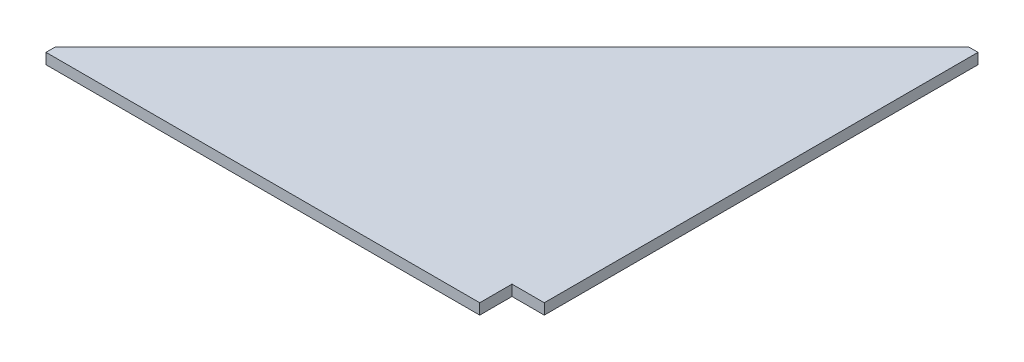
SolidWorks part; units mm, degrees
material "Pine"
ref_plane "Front Plane" through (0, 0, 0) normal (0, 0, 1) x (1, 0, 0)
ref_plane "Top Plane" through (0, 0, 0) normal (0, 1, 0) x (1, 0, 0)
ref_plane "Right Plane" through (0, 0, 0) normal (1, 0, 0) x (0, 0, -1)
sketch "Sketch1" plane through (0, 0, 0) normal (0, 1, 0) x (1, 0, 0)
  line L11 (-11.2, 550.1) -> (-550.1, 11.2)
  line L12 (0, 0) -> (-550.1, 0) construction
  line L13 (0, 0) -> (0, 550.1) construction
  line L14 (0, 550.1) -> (-550.1, 550.1) construction
  line L15 (-550.1, 0) -> (-550.1, 550.1) construction
  line L16 (0, 0) -> (-38.1, 0) construction
  line L17 (0, 0) -> (0, 38.1) construction
  line L18 (0, 38.1) -> (-38.1, 38.1) construction
  line L19 (-38.1, 0) -> (-38.1, 38.1) construction
  line L20 (-550.1, 11.2) -> (-550.1, 0)
  line L21 (-550.1, 0) -> (-38.1, 0)
  line L22 (-38.1, 0) -> (-38.1, 38.1)
  line L23 (-38.1, 38.1) -> (0, 38.1)
  line L24 (0, 38.1) -> (0, 550.1)
  line L25 (0, 550.1) -> (-11.2, 550.1)
  point P8 (-550.1, 11.2)
  point P9 (-11.2, 550.1)
  dimension "D1" = 550.1
  dimension "D2" = 550.1
  dimension "D3" = 38.1
  dimension "D4" = 38.1
  dimension "D5" = 11.2
  dimension "D6" = 11.2
extrude "Boss-Extrude1" add sketch "Sketch1" along normal blind 12.7
